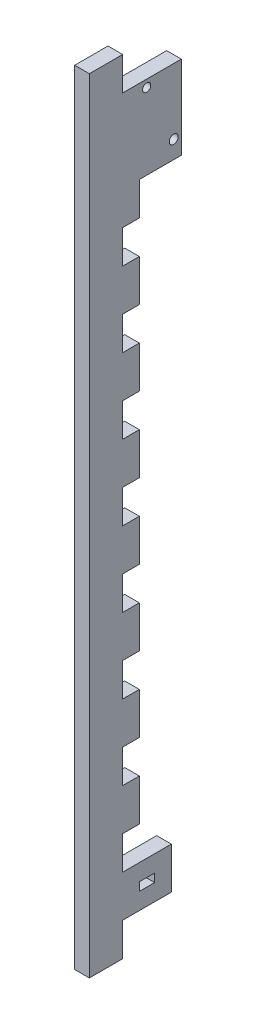
SolidWorks part; units mm, degrees
material "Acrylic (Medium-high impact)"
ref_plane "Front" through (0, 0, 0) normal (0, 0, 1) x (1, 0, 0)
ref_plane "Top" through (0, 0, 0) normal (0, 1, 0) x (1, 0, 0)
ref_plane "Right" through (0, 0, 0) normal (1, 0, 0) x (0, 0, -1)
sketch "Sketch1" plane through (0, 0, 0) normal (1, 0, 0) x (0, 0, -1)
  line L0 (9.525, 120.65) -> (9.525, 107.95)
  line L1 (-9.525, 149.225) -> (9.525, 149.225)
  line L2 (-9.525, 149.225) -> (-9.525, -149.225)
  line L3 (-9.525, -149.225) -> (9.525, -149.225)
  line L4 (9.525, 149.225) -> (9.525, -149.225)
  line L17 (9.525, 149.225) -> (3.175, 149.225)
  line L22 (9.525, 149.225) -> (9.525, 136.525)
  line L27 (9.525, 136.525) -> (3.175, 136.525)
  line L32 (3.175, 149.225) -> (3.175, 136.525)
  line L37 (9.525, 120.65) -> (3.175, 120.65)
  line L42 (3.175, 120.65) -> (3.175, 107.95)
  line L47 (9.525, 107.95) -> (3.175, 107.95)
  line L52 (9.525, 92.075) -> (9.525, 79.375)
  line L57 (9.525, 92.075) -> (3.175, 92.075)
  line L62 (3.175, 92.075) -> (3.175, 79.375)
  line L67 (9.525, 79.375) -> (3.175, 79.375)
  line L68 (9.525, 63.5) -> (9.525, 50.8)
  line L72 (9.525, 63.5) -> (3.175, 63.5)
  line L73 (3.175, 63.5) -> (3.175, 50.8)
  line L78 (9.525, 50.8) -> (3.175, 50.8)
  line L79 (9.525, 34.925) -> (9.525, 22.225)
  line L80 (9.525, 34.925) -> (3.175, 34.925)
  line L81 (3.175, 34.925) -> (3.175, 22.225)
  line L82 (9.525, 22.225) -> (3.175, 22.225)
  line L83 (9.525, 6.35) -> (9.525, -6.35)
  line L84 (9.525, 6.35) -> (3.175, 6.35)
  line L85 (3.175, 6.35) -> (3.175, -6.35)
  line L86 (9.525, -6.35) -> (3.175, -6.35)
  line L87 (9.525, -22.225) -> (9.525, -34.925)
  line L88 (9.525, -22.225) -> (3.175, -22.225)
  line L89 (3.175, -22.225) -> (3.175, -34.925)
  line L90 (9.525, -34.925) -> (3.175, -34.925)
  line L91 (9.525, -50.8) -> (9.525, -63.5)
  line L92 (9.525, -50.8) -> (3.175, -50.8)
  line L93 (3.175, -50.8) -> (3.175, -63.5)
  line L94 (9.525, -63.5) -> (3.175, -63.5)
  line L95 (9.525, -79.375) -> (9.525, -92.075)
  line L96 (9.525, -79.375) -> (3.175, -79.375)
  line L97 (3.175, -79.375) -> (3.175, -92.075)
  line L98 (9.525, -92.075) -> (3.175, -92.075)
  line L99 (9.525, -107.95) -> (9.525, -120.65)
  line L100 (9.525, -107.95) -> (3.175, -107.95)
  line L101 (3.175, -107.95) -> (3.175, -120.65)
  line L102 (9.525, -120.65) -> (3.175, -120.65)
  line L103 (9.525, -136.525) -> (9.525, -149.225)
  line L104 (9.525, -136.525) -> (3.175, -136.525)
  line L105 (3.175, -136.525) -> (3.175, -149.225)
  line L106 (9.525, -149.225) -> (3.175, -149.225)
  point P4 (0, -149.225)
  point P6 (-9.525, 0)
  dimension "D1" = 19.05
  dimension "D2" = 298.45
  dimension "D3" = 12.7
  dimension "D4" = 6.35
  dimension "D5" = 11
extrude "Boss-Extrude1" add sketch "Sketch1" along normal blind 5.588
sketch "Sketch2" plane through (5.588, 0, 0) normal (1, 0, 0) x (0, 0, -1)
  line L5 (9.525, -136.525) -> (3.175, -136.525) construction
  line L6 (9.525, -120.65) -> (21.717, -120.65)
  line L7 (9.525, -120.65) -> (9.525, -136.525)
  line L8 (9.525, -136.525) -> (21.717, -136.525)
  line L9 (21.717, -120.65) -> (21.717, -136.525)
  line L10 (25.425, 136.525) -> (25.425, 104.775) construction
  line L11 (9.525, -127) -> (15.367, -127)
  line L12 (9.525, -127) -> (9.525, -130.175)
  line L13 (9.525, -130.175) -> (15.367, -130.175)
  line L14 (15.367, -127) -> (15.367, -130.175)
  line L19 (3.175, 136.525) -> (25.525, 136.525)
  line L20 (3.175, 136.525) -> (3.175, 104.775)
  line L21 (3.175, 104.775) -> (25.525, 104.775)
  line L22 (25.525, 136.525) -> (25.525, 104.775)
  circle A1 centre (12.325, 133.725) radius 1.55
  circle A2 centre (22.625, 111.525) radius 1.7
  point P15 (5.975, 133.6675)
  point P22 (15.367, -128.5875)
  point P27 (21.717, -128.5875)
  line M21 (9.525, -136.525) -> (9.525, -120.65)
  line M55 (3.175, 107.95) -> (3.175, 120.65)
  line M56 (3.175, 120.65) -> (9.525, 120.65)
  line M57 (9.525, 120.65) -> (9.525, 136.525)
  line M58 (9.525, 136.525) -> (3.175, 136.525)
  dimension "D1" = 12.192
  dimension "D2" = 22.35
  dimension "D6" = 3.1
  dimension "D7" = 3.4
  dimension "D3" = 3.175
  dimension "D4" = 5.842
  dimension "D5" = 31.75
  dimension "D8" = 22.2
  dimension "D9" = 10.3
  dimension "D10" = 22.25
  dimension "D11" = 2.8
  dimension "D12" = 2.8
extrude "Boss-Extrude2" add sketch "Sketch2" against normal up to surface (5.588 mm away) contours L10 L19 L21 A2 M57 M56 M55 | L20 A1 M58 M56 M57 | L19 L10 L21 L22 | L11 L14 L13 L8 L9 L6 L7 M21
